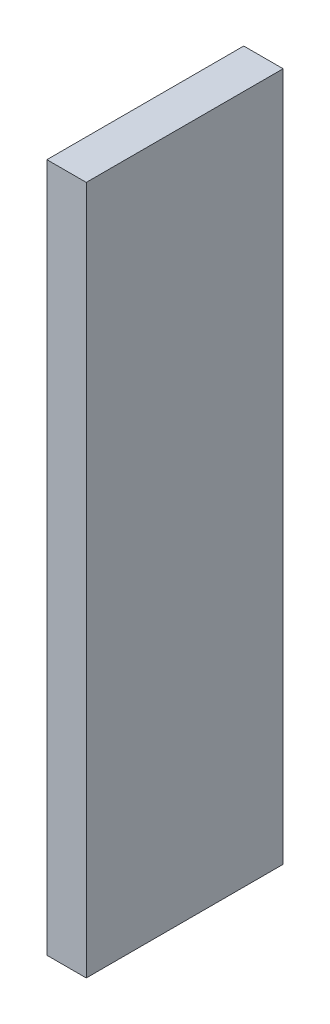
SolidWorks part; units mm, degrees
ref_plane "Piano frontale" through (0, 0, 0) normal (0, 0, 1) x (1, 0, 0)
ref_plane "Piano superiore" through (0, 0, 0) normal (0, 1, 0) x (1, 0, 0)
ref_plane "Piano destro" through (0, 0, 0) normal (1, 0, 0) x (0, 0, -1)
sketch "Schizzo1" plane through (0, 0, 0) normal (0, 0, 1) x (1, 0, 0)
  line L1 (0, 35) -> (-4, 35)
  line L2 (0, 35) -> (0, -35)
  line L3 (0, -35) -> (-4, -35)
  line L4 (-4, 35) -> (-4, -35)
  point P4 (0, 0)
  dimension "D1" = 70
  dimension "D2" = 4
extrude "Estrusione-Estrusione1" add sketch "Schizzo1" along normal blind 20
